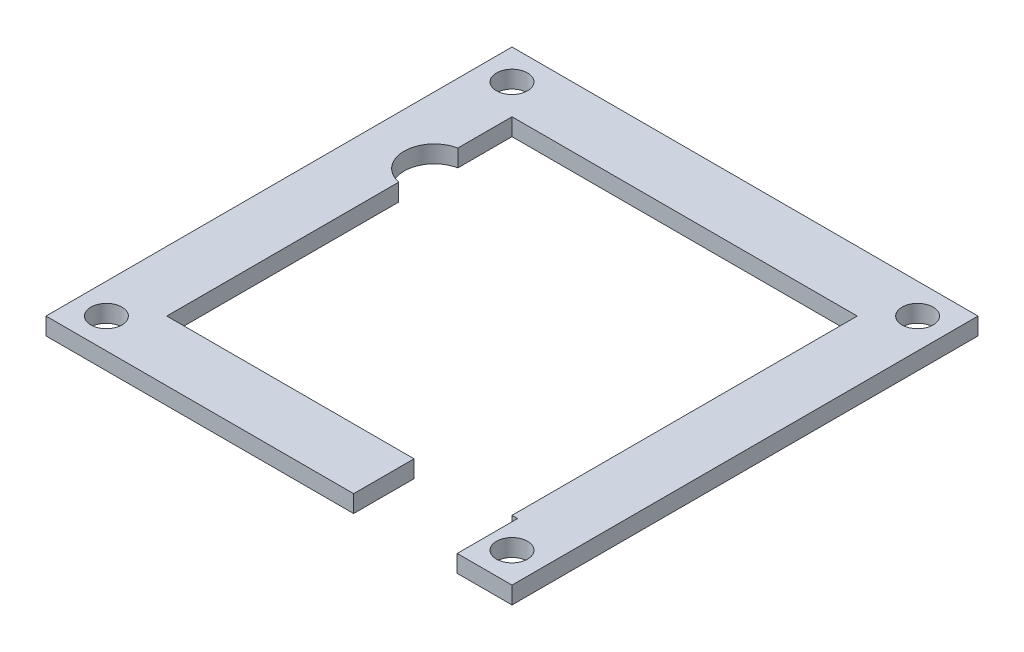
SolidWorks part; units mm, degrees
ref_plane "Front" through (0, 0, 0) normal (0, 0, 1) x (1, 0, 0)
ref_plane "Top" through (0, 0, 0) normal (0, 1, 0) x (1, 0, 0)
ref_plane "Right" through (0, 0, 0) normal (1, 0, 0) x (0, 0, -1)
sketch "草图3" plane through (0, 0, 0) normal (0, 1, 0) x (1, 0, 0)
  line L0 (16.9, -20) -> (20, -20)
  line L1 (-20, -20) -> (12.4, -20)
  line L2 (20, -20) -> (20, 20)
  line L3 (-27, 27) -> (-27, -27)
  line L4 (-27, -27) -> (27, -27)
  line L5 (27, -27) -> (27, 27)
  line L6 (27, 27) -> (-27, 27)
  line L7 (-8.6, 1.7) -> (-7.6812, 1.7)
  line L8 (-5.8437, 1.7) -> (-4.925, 1.7)
  line L9 (20.65, -20) -> (20, -20)
  line L10 (16.9, -6) -> (12.4, -6)
  line L11 (12.4, -6) -> (12.4, -19.5)
  line L12 (-10.4, 20) -> (-4.1, 20)
  line L13 (16.9, -6) -> (16.9, -19.5)
  line L14 (-20, 20) -> (-20, -20)
  line L15 (-3.0875, 1.7) -> (-2.1687, 1.7)
  line L16 (-0.3312, 1.7) -> (0.5875, 1.7)
  line L17 (2.425, 1.7) -> (3.3438, 1.7)
  line L18 (5.1813, 1.7) -> (6.1, 1.7)
  line L19 (8.8563, -13.3) -> (7.9375, -13.3)
  line L20 (8.65, -20) -> (8.65, -27)
  line L21 (-8.6, 1.7) -> (-8.6, -13.3)
  line L22 (-7.6812, -13.3) -> (-8.6, -13.3)
  line L23 (-8.6, -13.3) -> (-8.6029, -13.3589)
  line L24 (-10.4375, -13.3) -> (-11.3562, -13.3)
  line L25 (-10.4375, 1.7) -> (-11.3562, 1.7)
  line L26 (6.1, 1.7) -> (6.1, -13.3)
  line L27 (-4.925, -13.3) -> (-4.925, 1.7)
  line L28 (-11.3562, -13.3) -> (-11.3562, 1.7)
  line L29 (-3.0875, -13.3) -> (-3.0875, 1.7)
  line L30 (-10.4375, -13.3) -> (-10.4375, 1.7)
  line L31 (-2.1687, -13.3) -> (-2.1687, 1.7)
  line L32 (8.8563, 1.7) -> (7.9375, 1.7)
  line L33 (-5.8437, -13.3) -> (-5.8437, 1.7)
  line L34 (8.8563, -13.3) -> (8.8563, 1.7)
  line L35 (-7.6812, -13.3) -> (-7.6812, 1.7)
  line L36 (-0.3312, -13.3) -> (-0.3312, 1.7)
  line L37 (0.5875, -13.3) -> (0.5875, 1.7)
  line L38 (5.1813, -13.3) -> (6.1, -13.3)
  line L39 (2.425, -13.3) -> (2.425, 1.7)
  line L40 (3.3438, -13.3) -> (3.3438, 1.7)
  line L41 (2.425, -13.3) -> (3.3438, -13.3)
  line L42 (5.1813, -13.3) -> (5.1813, 1.7)
  line L43 (-0.3312, -13.3) -> (0.5875, -13.3)
  line L44 (-3.0875, -13.3) -> (-2.1687, -13.3)
  line L45 (-5.8437, -13.3) -> (-4.925, -13.3)
  line L46 (7.9375, -13.3) -> (7.9375, 1.7)
  line L47 (20.65, -20) -> (20.65, -27)
  line L48 (12.4, -19.5) -> (12.4, -20)
  line L49 (16.9, -19.5) -> (16.9, -20)
  line L50 (-20, -20) -> (20, -20) construction
  line L51 (-20, 20) -> (20, 20)
  line L52 (-16.7, 20) -> (-10.4, 20)
  line L53 (20, 20) -> (-20, 20) construction
  circle A0 centre (-23.5, -23.5) radius 1.8
  circle A1 centre (23.5, -23.5) radius 1.8
  circle A2 centre (-23.5, 23.5) radius 1.8
  circle A3 centre (23.5, 23.5) radius 1.8
  circle A4 centre (-2.1, -16.5) radius 2
  circle A5 centre (-16.4, -3.7) radius 2
  circle A6 centre (-19.3, 10.3) radius 2
  circle A7 centre (-1.1, 15.8) radius 2
  circle A8 centre (-19.3, 10.3) radius 3.5
  circle A9 centre (-16.4, -3.7) radius 3.5
  circle A10 centre (-2.1, -16.5) radius 3.4
  circle A11 centre (-1.1, 15.8) radius 3.5
  point P0 (0, 0)
  point P61 (-10.8969, 1.7)
  dimension "D1" = 7
extrude "凸台-拉伸2" add sketch "草图3" along normal blind 2
